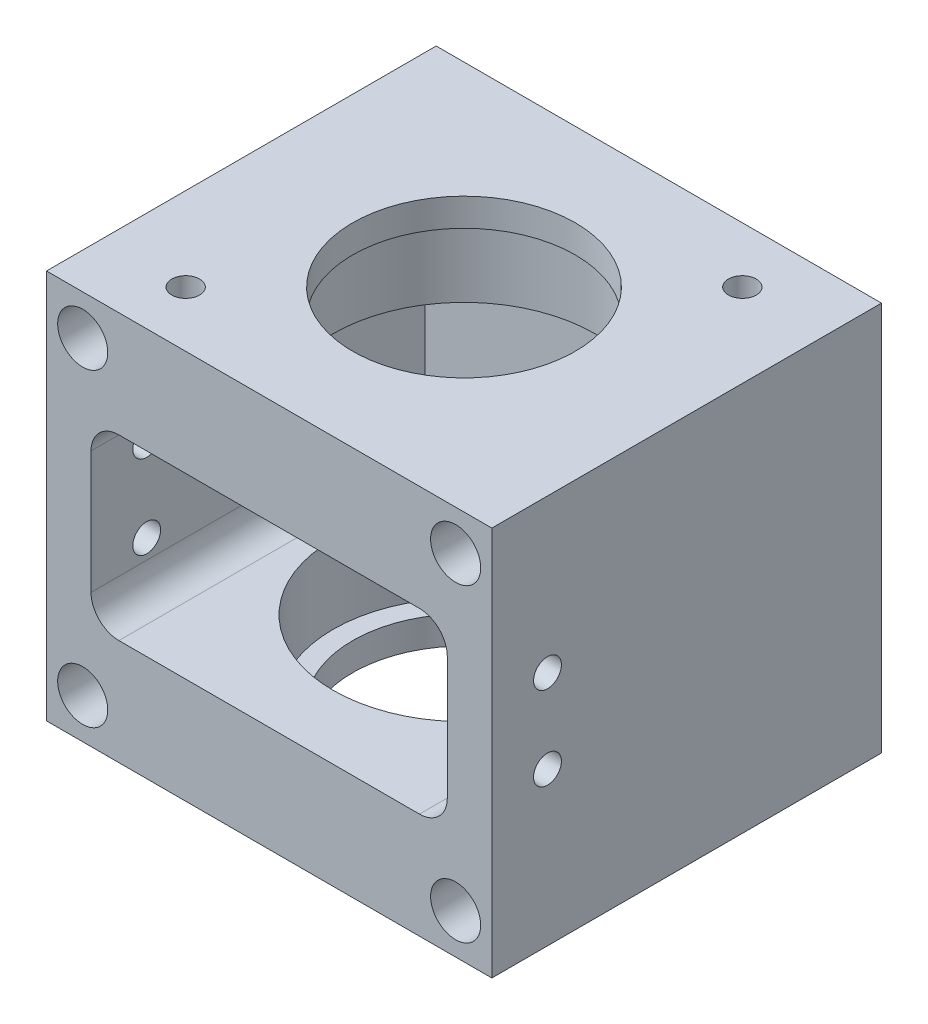
SolidWorks part; units mm, degrees
ref_plane "前视基准面" through (0, 0, 0) normal (0, 0, 1) x (1, 0, 0)
ref_plane "上视基准面" through (0, 0, 0) normal (0, 1, 0) x (1, 0, 0)
ref_plane "右视基准面" through (0, 0, 0) normal (1, 0, 0) x (0, 0, -1)
sketch "草图1" plane through (0, 0, 0) normal (0, 0, 1) x (1, 0, 0)
  line L1 (-40, 35) -> (40, 35)
  line L2 (-40, 35) -> (-40, -35)
  line L3 (-40, -35) -> (40, -35)
  line L4 (40, 35) -> (40, -35)
  line L5 (-40, 35) -> (40, -35) construction
  line L6 (-40, -35) -> (40, 35) construction
  point P0 (0, 0)
  dimension "D1" = 80
  dimension "D2" = 70
extrude "凸台-拉伸1" add sketch "草图1" along normal blind 70
sketch "草图2" plane through (0, 0, 70) normal (0, 0, 1) x (1, 0, 0)
  line L5 (-32, 16) -> (32, 16)
  line L6 (-32, 16) -> (-32, -16)
  line L7 (-32, -16) -> (32, -16)
  line L8 (32, 16) -> (32, -16)
  line L9 (-32, 16) -> (32, -16) construction
  line L10 (-32, -16) -> (32, 16) construction
  point P0 (0, 0)
  dimension "D1" = 64
  dimension "D2" = 32
extrude "切除-拉伸1" cut sketch "草图2" against normal blind 60
sketch "草图3" plane through (0, 0, 0) normal (0, 0, 1) x (1, 0, 0)
  line L1 (-33.5, 27.8) -> (33.5, 27.8) construction
  line L2 (-33.5, 27.8) -> (-33.5, -27.8) construction
  line L3 (-33.5, -27.8) -> (33.5, -27.8) construction
  line L4 (33.5, 27.8) -> (33.5, -27.8) construction
  line L5 (-33.5, 27.8) -> (33.5, -27.8) construction
  line L6 (-33.5, -27.8) -> (33.5, 27.8) construction
  circle A0 centre (-33.5, 27.8) radius 4.5
  circle A1 centre (33.5, 27.8) radius 4.5
  circle A2 centre (33.5, -27.8) radius 4.5
  circle A3 centre (-33.5, -27.8) radius 4.5
  point P0 (0, 0)
  dimension "D1" = 9
  dimension "D2" = 55.6
  dimension "D3" = 67
extrude "切除-拉伸5" cut sketch "草图3" along normal blind 100 contours A3 | A0 | A1 | A2
sketch "草图6" plane through (0, 0, 0) normal (0, 0, -1) x (-1, 0, 0)
  circle A0 centre (-33.5, 27.8) radius 5.5
  circle A1 centre (33.5, 27.8) radius 5.5
  circle A2 centre (33.5, -27.8) radius 5.5
  circle A3 centre (-33.5, -27.8) radius 5.5
  dimension "D1" = 11
extrude "切除-拉伸7" cut sketch "草图6" against normal blind 30
sketch "草图5" plane through (-5, 35, 0) normal (0, -1, 0) x (0, 0, 1)
  line L0 (70, -45) -> (70, 35) construction
  circle A0 centre (35, -5) radius 20
  dimension "D1" = 40
  dimension "D2" = 35
  dimension "D3" = 0
extrude "切除-拉伸8" cut sketch "草图5" along normal blind 87 contours A0
sketch "草图7" plane through (0, 16, 0) normal (0, -1, 0) x (1, 0, 0)
  circle A0 centre (0, 35) radius 23.5
  dimension "D1" = 47
extrude "切除-拉伸9" cut sketch "草图7" against normal blind 14
ref_plane "基准面1" through (0, 0, 0) normal (0, -1, 0) x (-1, 0, 0)
mirror "镜向1" about plane through (0, 0, 0) normal (0, -1, 0) of "切除-拉伸9"
fillet "圆角1" radius 5 4 edges at (32, -16, 40) (32, 16, 40) (-32, 16, 40) (-32, -16, 40)
sketch "草图8" plane through (-40, 0, 0) normal (-1, 0, 0) x (0, 0, 1)
  line L0 (60, 7.5) -> (60, -7.5) construction
hole_wizard "M6 螺纹孔1" positions "3D草图1" profile "草图10" tap size "M6" standard "GB" end condition through all
sketch3d "3D草图1"
  point P0 (-40, 7.5, 60)
  point P3 (-40, -7.5, 60)
sketch "草图10" plane through (-40, 7.5, 60) normal (0, 1, 0) x (0, 0, 1)
  line L0 (0, 0) -> (0, 80)
  line L1 (0, 80) -> (2.5, 80)
  line L2 (2.5, 80) -> (2.5, 0)
  line L5 (2.5, 0) -> (0, 0)
  line L11 (0, -6.35) -> (0, 107.95) construction
  dimension "通孔螺纹孔钻头直径" = 5
  dimension "通孔螺纹孔钻头深度" = 80
cosmetic thread "孔螺蚊线1" parameters "D2"=6
cosmetic thread "孔螺蚊线2" parameters "D2"=6
sketch "草图11" plane through (0, 35, 0) normal (0, 1, 0) x (1, 0, 0)
  line L1 (25, -10) -> (-25, -10)
  line L2 (25, -10) -> (25, -60)
  line L3 (25, -60) -> (-25, -60)
  line L4 (-25, -10) -> (-25, -60)
  line L5 (25, -10) -> (-25, -60) construction
  line L6 (25, -60) -> (-25, -10) construction
  point P0 (0, -35)
  dimension "D1" = 50
hole_wizard "M6 螺纹孔2" positions "3D草图2" profile "草图13" tap size "M6" standard "GB"
sketch3d "3D草图2"
  point P0 (25, 35, 10)
  point P3 (-25, 35, 60)
sketch "草图13" plane through (25, 35, 10) normal (1, 0, 0) x (0, 0, 1)
  line L0 (0, 0) -> (0, 11.5022)
  line L1 (0, 11.5022) -> (2.5, 10)
  line L2 (2.5, 10) -> (2.5, 0)
  line L5 (2.5, 0) -> (0, 0)
  line L10 (0, 11.5022) -> (-2.5, 10) construction
  line L11 (0, -6.35) -> (0, 107.95) construction
  dimension "螺纹孔钻头直径" = 5
  dimension "螺纹孔钻头深度" = 10
  dimension "导头角度" = 118
cosmetic thread "孔螺蚊线3" parameters "D1"=10, "D2"=6
cosmetic thread "孔螺蚊线4" parameters "D1"=10, "D2"=6
sketch "草图14" plane through (0, -35, 0) normal (0, -1, 0) x (1, 0, 0)
  line L1 (-25, 60) -> (25, 60)
  line L2 (-25, 60) -> (-25, 10)
  line L3 (-25, 10) -> (25, 10)
  line L4 (25, 60) -> (25, 10)
  line L5 (-25, 60) -> (25, 10) construction
  line L6 (-25, 10) -> (25, 60) construction
  point P0 (0, 35)
  dimension "D1" = 50
hole_wizard "M6 螺纹孔3" positions "3D草图3" profile "草图15" tap size "M6" standard "GB"
sketch3d "3D草图3"
  point P0 (-25, -35, 60)
  point P3 (25, -35, 60)
  point P6 (25, -35, 10)
  point P9 (-25, -35, 10)
sketch "草图15" plane through (-25, -35, 60) normal (1, 0, 0) x (0, 0, -1)
  line L0 (0, 0) -> (0, 16.5022)
  line L1 (0, 16.5022) -> (2.5, 15)
  line L2 (2.5, 15) -> (2.5, 0)
  line L5 (2.5, 0) -> (0, 0)
  line L10 (0, 16.5022) -> (-2.5, 15) construction
  line L11 (0, -6.35) -> (0, 107.95) construction
  dimension "螺纹孔钻头直径" = 5
  dimension "螺纹孔钻头深度" = 15
  dimension "导头角度" = 118
cosmetic thread "孔螺蚊线5" parameters "D1"=12, "D2"=6
cosmetic thread "孔螺蚊线6" parameters "D1"=12, "D2"=6
cosmetic thread "孔螺蚊线7" parameters "D1"=12, "D2"=6
cosmetic thread "孔螺蚊线8" parameters "D1"=12, "D2"=6
